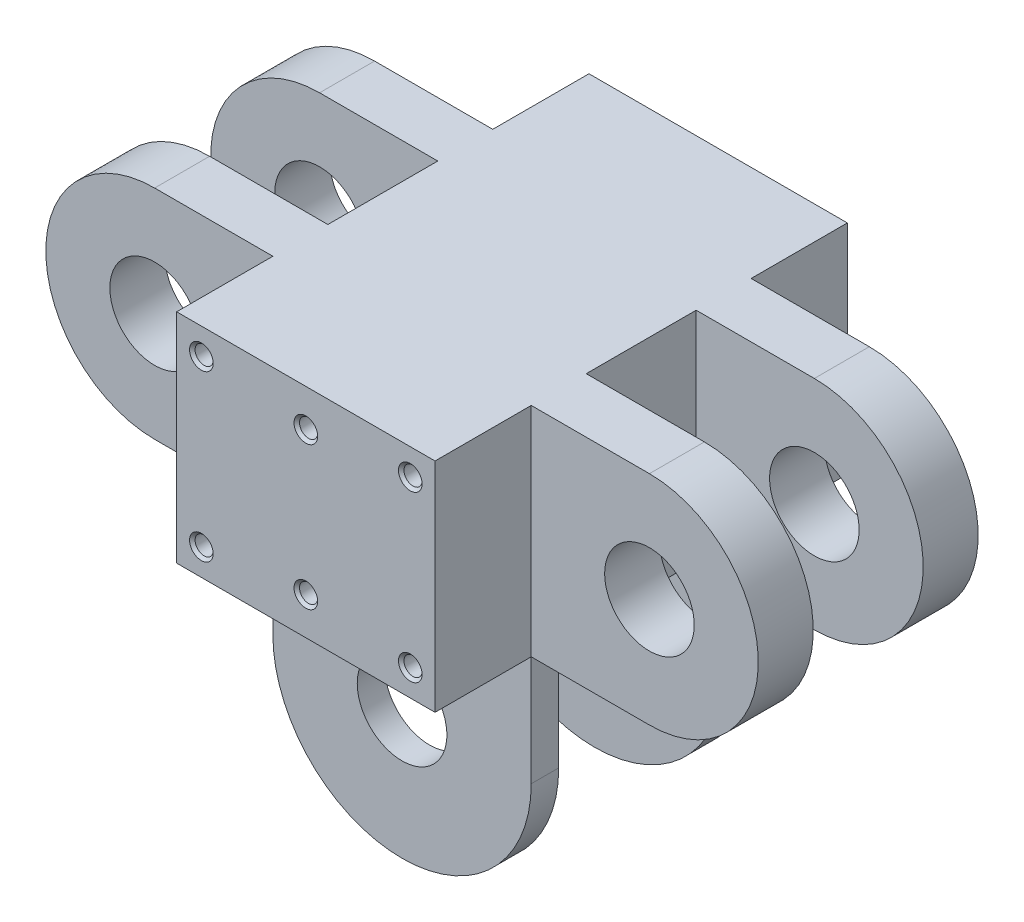
SolidWorks part; units mm, degrees
ref_plane "Płaszczyzna przednia" through (0, 0, 0) normal (0, 0, 1) x (1, 0, 0)
ref_plane "Płaszczyzna górna" through (0, 0, 0) normal (0, 1, 0) x (1, 0, 0)
ref_plane "Płaszczyzna prawa" through (0, 0, 0) normal (1, 0, 0) x (0, 0, -1)
sketch "Szkic1" plane through (0, 0, 0) normal (0, 0, 1) x (1, 0, 0)
  line L8 (47, 19.8) -> (0, 19.8) construction
  line L11 (0, 0) -> (47, 0)
  line L12 (0, 0) -> (0, 39.6)
  line L13 (0, 39.6) -> (47, 39.6)
  line L14 (47, 0) -> (47, 39.6)
  dimension "D1" = 39.6
  dimension "D4" = 47
extrude "Dodanie-wyciągnięcie3" add sketch "Szkic1" along normal blind 75
ref_plane "Płaszczyzna1" through (0, 0, 37.5) normal (0, 0, -1) x (-1, 0, 0)
ref_plane "Płaszczyzna2" through (0, 0, 27.5) normal (0, 0, -1) x (-1, 0, 0)
sketch "Szkic4" plane through (0, 0, 27.5) normal (0, 0, -1) x (-1, 0, 0)
  line L0 (-47, 39.6) -> (-68.5, 39.6)
  line L2 (-68.5, 0) -> (-47, 0)
  line L3 (-47, 39.6) -> (0, 39.6) construction
  line L5 (-23.5, 39.6) -> (-23.5, 0) construction
  line L10 (-47, 39.6) -> (-47, 0)
  line L11 (-47, 0) -> (0, 0) construction
  line L12 (21.5, 0) -> (0, 0)
  line L13 (0, 39.6) -> (0, 0)
  line L14 (0, 39.6) -> (21.5, 39.6)
  arc A4 (-68.5, 39.6) -> (-68.5, 0) centre (-68.5, 19.8) ccw
  circle A5 centre (-68.5, 19.8) radius 8.15
  arc A6 (21.5, 39.6) -> (21.5, 0) centre (21.5, 19.8) cw
  circle A7 centre (21.5, 19.8) radius 8.15
  dimension "D1" = 90
  dimension "D4" = 16.3
  dimension "D5" = 19.8
extrude "Dodanie-wyciągnięcie4" add sketch "Szkic4" along normal blind 10
mirror "Lustro1" about plane through (0, 0, 37.5) normal (0, 0, -1) of "Dodanie-wyciągnięcie4"
ref_plane "Płaszczyzna3" through (0, 0, 22.5) normal (0, 0, -1) x (-1, 0, 0)
sketch "Szkic5" plane through (0, 0, 22.5) normal (0, 0, -1) x (-1, 0, 0)
  line L0 (-47, 0) -> (0, 0)
  line L1 (0, 0) -> (0, -20)
  line L2 (-47, 0) -> (-47, -20)
  line L3 (-47, -20) -> (0, -20) construction
  arc A0 (-47, -20) -> (0, -20) centre (-23.5, -20) ccw
  circle A1 centre (-23.5, -20) radius 8.15
  dimension "D1" = 16.3
  dimension "D2" = 20
extrude "Dodanie-wyciągnięcie5" add sketch "Szkic5" along normal blind 5
mirror "Lustro2" about plane through (0, 0, 37.5) normal (0, 0, -1) of "Dodanie-wyciągnięcie5"
sketch "Szkic6" plane through (0, 0, 75) normal (0, 0, 1) x (1, 0, 0)
  line L0 (0, 19.8) -> (47, 19.8) construction
  line L1 (0, 39.6) -> (0, 0) construction
  line L2 (47, 39.6) -> (47, 0) construction
  line L3 (23.5, 34.8) -> (23.5, 4.8) construction
  line L4 (4.5, 4.8) -> (42.5, 4.8) construction
  line L5 (4.5, 4.8) -> (4.5, 34.8) construction
  line L6 (4.5, 34.8) -> (42.5, 34.8) construction
  line L7 (42.5, 4.8) -> (42.5, 34.8) construction
  line L8 (4.5, 4.8) -> (42.5, 34.8) construction
  line L9 (4.5, 34.8) -> (42.5, 4.8) construction
  circle A0 centre (4.5, 4.8) radius 1.65
  circle A1 centre (4.5, 34.8) radius 1.65
  circle A2 centre (42.5, 34.8) radius 1.65
  circle A3 centre (42.5, 4.8) radius 1.65
  circle A4 centre (23.5, 32.8) radius 1.65
  circle A5 centre (23.5, 6.8) radius 1.65
  point P6 (23.5, 19.8)
  dimension "D1" = 3.3
  dimension "D4" = 26
  dimension "D2" = 38
  dimension "D3" = 30
  dimension "D5" = 13
hole_wizard "Otwór gwintowany M4x0.71" positions "Szkic7" profile "Szkic8" tap size "M4x0.7" standard "Ansi Metric"
sketch "Szkic7" plane through (0, 0, 75) normal (0, 0, 1) x (1, 0, 0)
  point P0 (4.5, 34.8)
  point P3 (23.5, 32.8)
  point P6 (42.5, 34.8)
  point P9 (42.5, 4.8)
  point P12 (23.5, 6.8)
  point P15 (4.5, 4.8)
sketch "Szkic8" plane through (4.5, 34.8, 75) normal (1, 0, 0) x (0, -1, 0)
  line L0 (0, 0) -> (0, 15.9914)
  line L1 (0, 15.9914) -> (1.65, 15)
  line L2 (1.65, 15) -> (1.65, 0)
  line L5 (1.65, 0) -> (0, 0)
  line L10 (0, 15.9914) -> (-1.65, 15) construction
  line L11 (0, -6.35) -> (0, 107.95) construction
  dimension "Średnica wiertła gwintu" = 3.3
  dimension "Głębokość otworu gwintowanego" = 15
  dimension "Kąt wiertła" = 118
cosmetic thread "Gwint otworu1" parameters "D1"=12, "D2"=4
cosmetic thread "Gwint otworu2" parameters "D1"=12, "D2"=4
cosmetic thread "Gwint otworu3" parameters "D1"=12, "D2"=4
cosmetic thread "Gwint otworu4" parameters "D1"=12, "D2"=4
cosmetic thread "Gwint otworu5" parameters "D1"=12, "D2"=4
cosmetic thread "Gwint otworu6" parameters "D1"=12, "D2"=4
chamfer "Sfazowanie1" distance 0.5 angle 45 6 edges at (6.15, 4.8, 75) (25.15, 6.8, 75) (44.15, 4.8, 75) (44.15, 34.8, 75) (25.15, 32.8, 75) (6.15, 34.8, 75)
